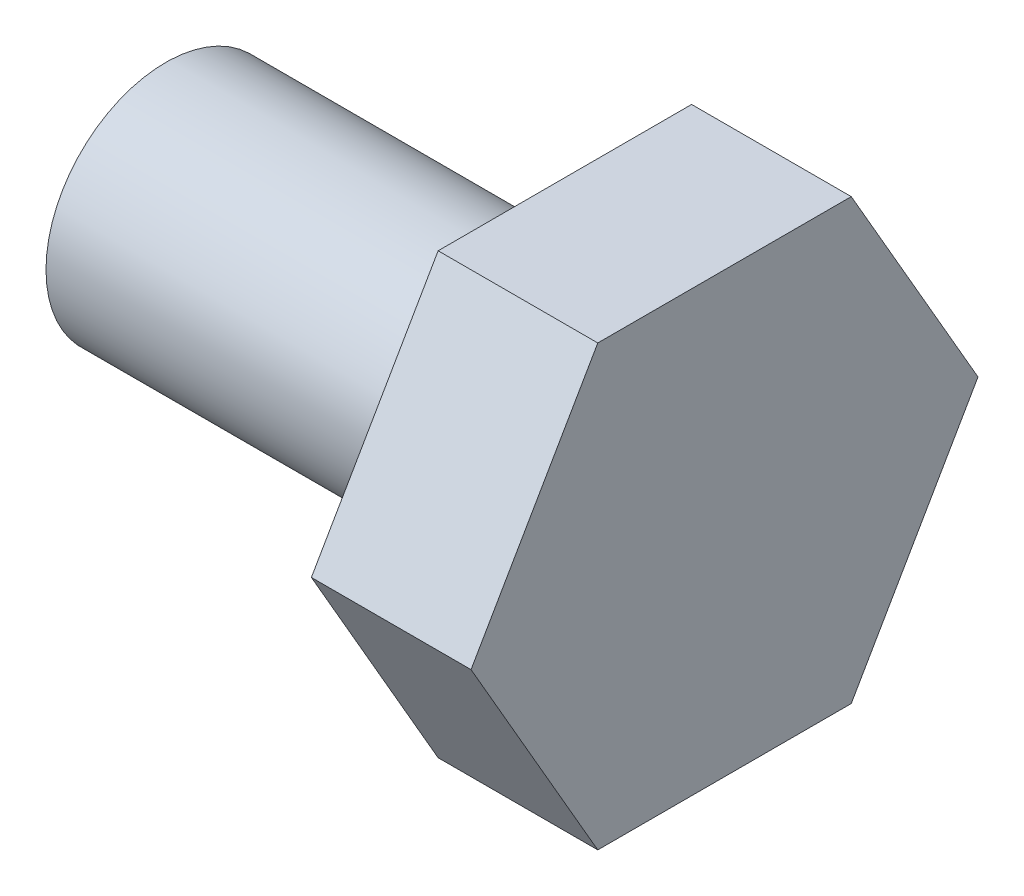
SolidWorks part; units mm, degrees
material "Plain Carbon Steel"
ref_plane "Front Plane" through (0, 0, 0) normal (0, 0, 1) x (1, 0, 0)
ref_plane "Top Plane" through (0, 0, 0) normal (0, 1, 0) x (1, 0, 0)
ref_plane "Right Plane" through (0, 0, 0) normal (1, 0, 0) x (0, 0, -1)
sketch "Sketch1" plane through (0, 0, 0) normal (0, 0, 1) x (1, 0, 0)
  line L0 (-16.1666, 0) -> (19.5323, 0) construction
  line L1 (-2.5, 0) -> (2.5, 0)
  line L2 (-2.5, 0) -> (-2.5, 1.5)
  line L3 (-2.5, 1.5) -> (2.5, 1.5)
  line L4 (2.5, 0) -> (2.5, 1.5)
  dimension "D1" = 3
  dimension "D2" = 5
revolve "Revolve1" add sketch "Sketch1" angle 360 about L0
sketch "Sketch2" plane through (2.5, 0, 0) normal (1, 0, 0) x (0, 0, -1)
  line L1 (1.5877, 2.75) -> (-1.5877, 2.75)
  line L2 (-1.5877, 2.75) -> (-3.1754, 0)
  line L3 (-3.1754, 0) -> (-1.5877, -2.75)
  line L4 (-1.5877, -2.75) -> (1.5877, -2.75)
  line L5 (1.5877, -2.75) -> (3.1754, 0)
  line L6 (3.1754, 0) -> (1.5877, 2.75)
  circle A0 centre (0, 0) radius 2.75 construction
  dimension "D1" = 5.5
extrude "Boss-Extrude1" add sketch "Sketch2" along normal blind 2
